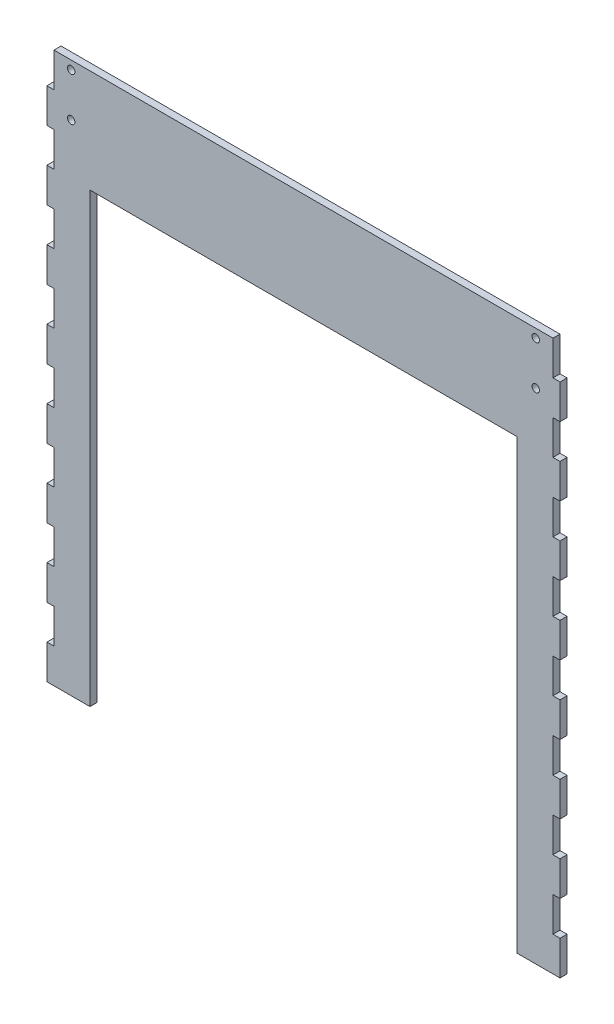
SolidWorks part; units mm, degrees
ref_plane "Front Plane" through (0, 0, 0) normal (0, 0, 1) x (1, 0, 0)
ref_plane "Top Plane" through (0, 0, 0) normal (0, 1, 0) x (1, 0, 0)
ref_plane "Right Plane" through (0, 0, 0) normal (1, 0, 0) x (0, 0, -1)
sketch "Sketch1" plane through (0, 0, 0) normal (0, 0, 1) x (1, 0, 0)
  line L0 (-184.15, 406.4) -> (-184.15, 0) construction
  line L1 (-189.357, 0) -> (189.357, 0)
  line L2 (-189.357, 0) -> (-189.357, 406.4)
  line L3 (-189.357, 406.4) -> (189.357, 406.4)
  line L4 (189.357, 0) -> (189.357, 406.4)
  line L5 (184.15, 0) -> (184.15, 406.4) construction
  line L7 (-157.607, 0) -> (157.607, 0)
  line L8 (-157.607, 0) -> (-157.607, 330.2)
  line L9 (-157.607, 330.2) -> (157.607, 330.2)
  line L10 (157.607, 0) -> (157.607, 330.2)
  line L12 (-184.15, 406.4) -> (-184.15, 381)
  line L13 (189.357, 406.4) -> (184.15, 406.4)
  line L14 (189.357, 406.4) -> (189.357, 381)
  line L15 (189.357, 381) -> (184.15, 381)
  line L16 (184.15, 406.4) -> (184.15, 381)
  line L17 (-184.15, 406.4) -> (-189.357, 406.4)
  line L18 (-189.357, 406.4) -> (-189.357, 381)
  line L19 (-184.15, 381) -> (-189.357, 381)
  line L20 (-184.15, 355.6) -> (-184.15, 330.2)
  line L21 (-184.15, 355.6) -> (-189.357, 355.6)
  line L22 (-189.357, 355.6) -> (-189.357, 330.2)
  line L23 (-184.15, 330.2) -> (-189.357, 330.2)
  line L24 (-184.15, 304.8) -> (-184.15, 279.4)
  line L25 (-184.15, 304.8) -> (-189.357, 304.8)
  line L26 (-189.357, 304.8) -> (-189.357, 279.4)
  line L27 (-184.15, 279.4) -> (-189.357, 279.4)
  line L28 (-184.15, 254) -> (-184.15, 228.6)
  line L29 (-184.15, 254) -> (-189.357, 254)
  line L30 (-189.357, 254) -> (-189.357, 228.6)
  line L31 (-184.15, 228.6) -> (-189.357, 228.6)
  line L32 (-184.15, 203.2) -> (-184.15, 177.8)
  line L33 (-184.15, 203.2) -> (-189.357, 203.2)
  line L34 (-189.357, 203.2) -> (-189.357, 177.8)
  line L35 (-184.15, 177.8) -> (-189.357, 177.8)
  line L36 (-184.15, 152.4) -> (-184.15, 127)
  line L37 (-184.15, 152.4) -> (-189.357, 152.4)
  line L38 (-189.357, 152.4) -> (-189.357, 127)
  line L39 (-184.15, 127) -> (-189.357, 127)
  line L40 (-184.15, 101.6) -> (-184.15, 76.2)
  line L41 (-184.15, 101.6) -> (-189.357, 101.6)
  line L42 (-189.357, 101.6) -> (-189.357, 76.2)
  line L43 (-184.15, 76.2) -> (-189.357, 76.2)
  line L44 (-184.15, 50.8) -> (-184.15, 25.4)
  line L45 (-184.15, 50.8) -> (-189.357, 50.8)
  line L46 (-189.357, 50.8) -> (-189.357, 25.4)
  line L47 (-184.15, 25.4) -> (-189.357, 25.4)
  line L48 (189.357, 355.6) -> (189.357, 330.2)
  line L49 (189.357, 355.6) -> (184.15, 355.6)
  line L50 (184.15, 355.6) -> (184.15, 330.2)
  line L51 (189.357, 330.2) -> (184.15, 330.2)
  line L52 (189.357, 304.8) -> (189.357, 279.4)
  line L53 (189.357, 304.8) -> (184.15, 304.8)
  line L54 (184.15, 304.8) -> (184.15, 279.4)
  line L55 (189.357, 279.4) -> (184.15, 279.4)
  line L56 (189.357, 254) -> (189.357, 228.6)
  line L57 (189.357, 254) -> (184.15, 254)
  line L58 (184.15, 254) -> (184.15, 228.6)
  line L59 (189.357, 228.6) -> (184.15, 228.6)
  line L60 (189.357, 203.2) -> (189.357, 177.8)
  line L61 (189.357, 203.2) -> (184.15, 203.2)
  line L62 (184.15, 203.2) -> (184.15, 177.8)
  line L63 (189.357, 177.8) -> (184.15, 177.8)
  line L64 (189.357, 152.4) -> (189.357, 127)
  line L65 (189.357, 152.4) -> (184.15, 152.4)
  line L66 (184.15, 152.4) -> (184.15, 127)
  line L67 (189.357, 127) -> (184.15, 127)
  line L68 (189.357, 101.6) -> (189.357, 76.2)
  line L69 (189.357, 101.6) -> (184.15, 101.6)
  line L70 (184.15, 101.6) -> (184.15, 76.2)
  line L71 (189.357, 76.2) -> (184.15, 76.2)
  line L72 (189.357, 50.8) -> (189.357, 25.4)
  line L73 (189.357, 50.8) -> (184.15, 50.8)
  line L74 (184.15, 50.8) -> (184.15, 25.4)
  line L75 (189.357, 25.4) -> (184.15, 25.4)
  circle A0 centre (-171.45, 400.05) radius 2.75
  circle A1 centre (-171.45, 368.05) radius 2.75
  circle A2 centre (171.45, 400.05) radius 2.75
  circle A3 centre (171.45, 368.05) radius 2.75
  point P5 (0, 0)
  point P16 (0, 330.2)
  point P17 (-189.357, 203.2)
  point P22 (186.7535, 355.6)
  dimension "D4" = 5.5
  dimension "D2" = 406.4
  dimension "D3" = 12.7
  dimension "D5" = 5.207
  dimension "D6" = 6.35
  dimension "D7" = 32
  dimension "D8" = 5.207
  dimension "D9" = 12.7
  dimension "D10" = 368.3
  dimension "D11" = 31.75
  dimension "D12" = 76.2
  dimension "D13" = 25.4
  dimension "D16" = 25.4
  dimension "D14" = 2
  dimension "D15" = 8
extrude "Boss-Extrude1" add sketch "Sketch1" along normal blind 5.207
